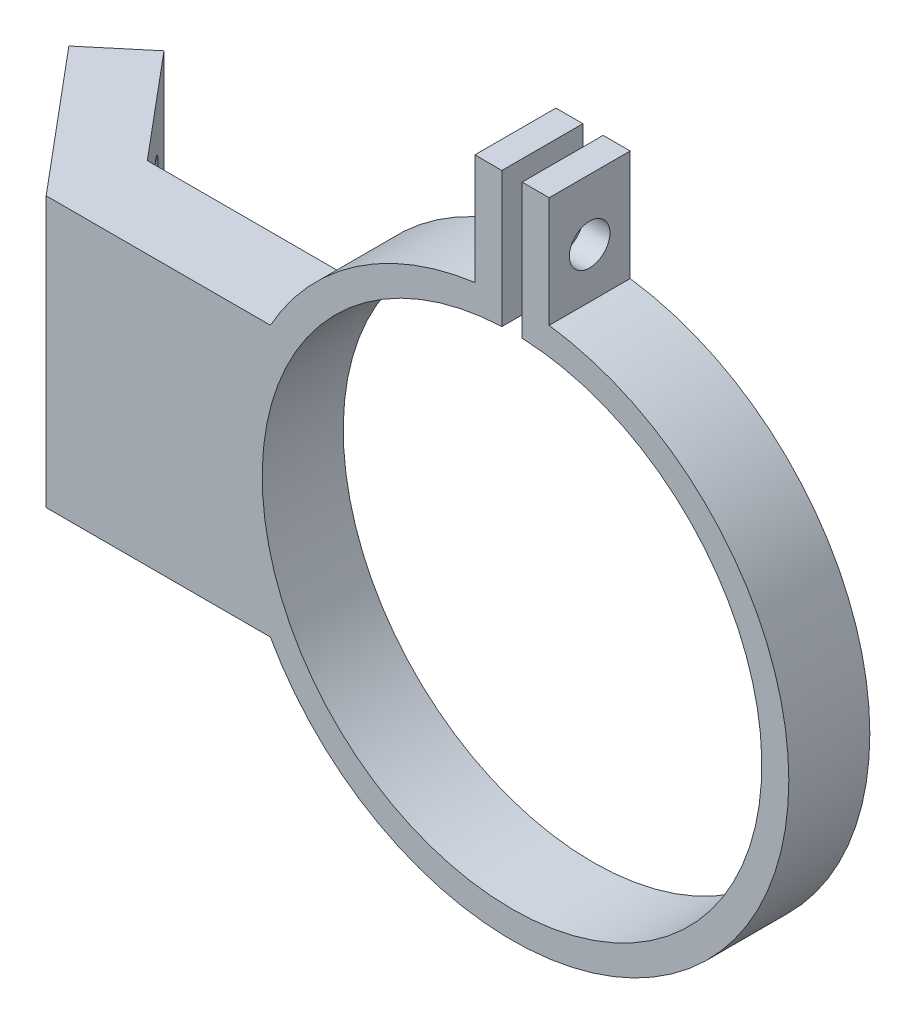
SolidWorks part; units mm, degrees
ref_plane "Front Plane" through (0, 0, 0) normal (0, 0, 1) x (1, 0, 0)
ref_plane "Top Plane" through (0, 0, 0) normal (0, 1, 0) x (1, 0, 0)
ref_plane "Right Plane" through (0, 0, 0) normal (1, 0, 0) x (0, 0, -1)
sketch "Sketch1" plane through (0, 0, 0) normal (0, 0, 1) x (1, 0, 0)
  line L0 (0, 44.9312) -> (0, -79.2184) construction
  line L1 (-88.7321, 0) -> (94.949, 0) construction
  line L2 (-2.75, 28.5) -> (2.75, 28.5) construction
  line L3 (2.75, 28.5) -> (2.75, 18.2945)
  line L5 (-2.75, 18.2945) -> (-2.75, 28.5)
  line L6 (-0.75, 28.5) -> (-0.75, 18.4848)
  line L7 (-0.75, 28.5) -> (0.75, 28.5) construction
  line L8 (0.75, 28.5) -> (0.75, 18.4848)
  line L9 (-2.75, 28.5) -> (-0.75, 28.5)
  line L10 (0.75, 28.5) -> (2.75, 28.5)
  line L11 (-20.5, 10) -> (-17.8955, 10)
  line L12 (-2.75, 22.5) -> (2.75, 22.5) construction
  line L13 (-2.75, 22.5) -> (-2.75, 25.5)
  line L14 (-2.75, 25.5) -> (2.75, 25.5) construction
  line L15 (2.75, 22.5) -> (2.75, 25.5)
  line L16 (-2.75, 22.5) -> (2.75, 25.5) construction
  line L17 (-2.75, 25.5) -> (2.75, 22.5) construction
  line L18 (-34.5, -10) -> (-20.5, -10)
  line L19 (-34.5, -10) -> (-34.5, 10)
  line L20 (-34.5, 10) -> (-20.5, 10)
  line L21 (-20.5, -10) -> (-20.5, 10) construction
  line L22 (-34.5, -10) -> (-20.5, 10) construction
  line L23 (-34.5, 10) -> (-20.5, -10) construction
  line L24 (-20.5, -10) -> (-17.8955, -10)
  circle A0 centre (0, 0) radius 18.5
  circle A1 centre (0, 0) radius 20.5
  point P8 (0, 28.5)
  point P15 (0, 28.5)
  point P18 (0, 24)
  point P23 (-27.5, 0)
  dimension "D1" = 37
  dimension "D2" = 2
  dimension "D3" = 3
  dimension "D4" = 24
  dimension "D5" = 3
  dimension "D6" = 2
  dimension "D7" = 1.5
  dimension "D8" = 20
  dimension "D9" = 14
extrude "Boss-Extrude1" add sketch "Sketch1" along normal mid plane 6 contours L5 A1 L3 A0 | L3 A1 L8 A0 | L6 A1 L5 A0 | A1 L6 L9 L5 | A1 L3 L10 L8 | A1 L11 L20 L19 L18 L24
sketch "Sketch2" plane through (0, 0, 0) normal (1, 0, 0) x (0, 0, -1)
  circle A0 centre (0, 24) radius 1.5
  point P2 (0, 0)
  dimension "D1" = 3
extrude "Cut-Extrude1" cut sketch "Sketch2" against normal through all both and the other way through all
sketch "Sketch3" plane through (0, 0, 0) normal (0, 1, 0) x (1, 0, 0)
  line L0 (-34.5, -3) -> (-43.2657, 7.4465)
  line L1 (-43.2657, 7.4465) -> (-39.4354, 10.6604)
  line L2 (-39.4354, 10.6604) -> (-33.0076, 3)
  line L3 (-34.5, 3) -> (-17.8955, 3) construction
  line L4 (-34.5, -3) -> (-33.0076, 3)
  line L5 (-34.5, 0) -> (-20.5, 0) construction
  dimension "D1" = 5
  dimension "D2" = 50
  dimension "D3" = 10
extrude "Boss-Extrude2" add sketch "Sketch3" along normal up to surface and the other way up to surface up to face at (-26.1978, 10, 0) other way up to face at (-26.1978, -10, 0)
sketch "Sketch4" plane through (-17.8924, 0, 15.0135) normal (0.766, 0, -0.6428) x (-0.6428, 0, -0.766)
  line L0 (28.515, 5) -> (28.515, -5) construction
  line L1 (128614.5579, 0) -> (-128618.554, 0) construction
  line L2 (33.515, 10) -> (33.515, -10) construction
  circle A0 centre (28.515, 5) radius 1.5
  circle A1 centre (28.515, -5) radius 1.5
  point P4 (28.515, 0)
  point P5 (25.8922, 4.3435)
  dimension "D1" = 3
  dimension "D2" = 10
  dimension "D3" = 5
extrude "Cut-Extrude2" cut sketch "Sketch4" against normal through all both and the other way through all
